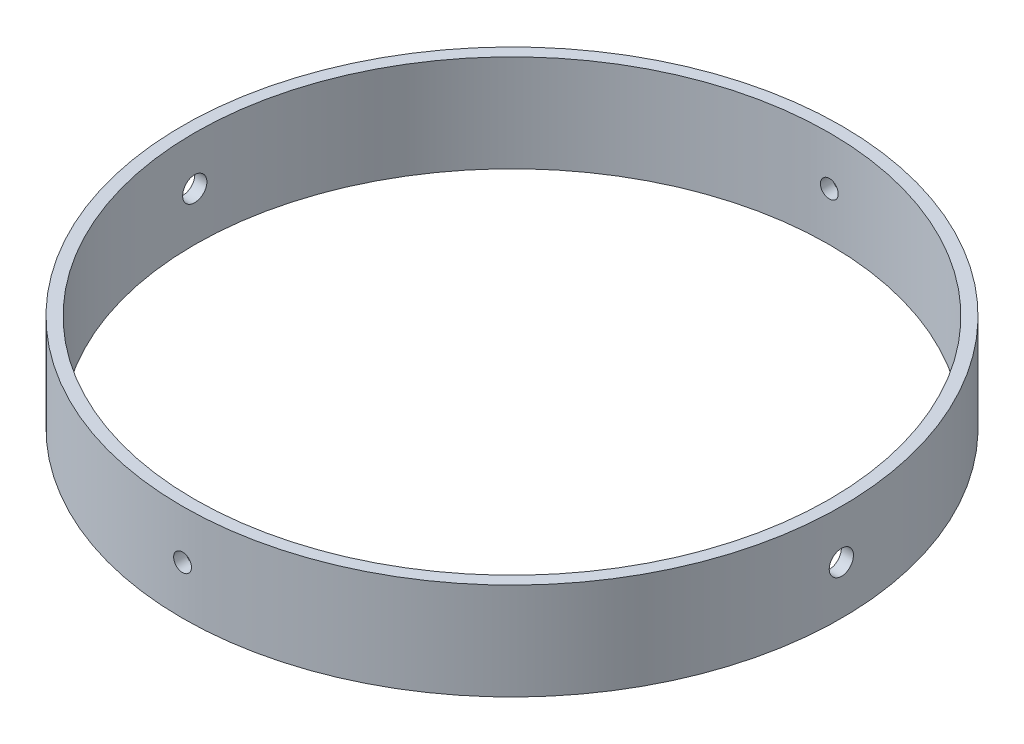
SolidWorks part; units mm, degrees
ref_plane "Front Plane" through (0, 0, 0) normal (0, 0, 1) x (1, 0, 0)
ref_plane "Top Plane" through (0, 0, 0) normal (0, 1, 0) x (1, 0, 0)
ref_plane "Right Plane" through (0, 0, 0) normal (1, 0, 0) x (0, 0, -1)
sketch "Sketch1" plane through (0, 0, 0) normal (0, 1, 0) x (1, 0, 0)
  circle A0 centre (0, 0) radius 86.36
  circle A1 centre (0, 0) radius 83.185
  dimension "D1" = 172.72
  dimension "D2" = 166.37
extrude "Boss-Extrude1" add sketch "Sketch1" along normal blind 25.4
sketch "Sketch2" plane through (0, 0, 0) normal (1, 0, 0) x (0, 0, -1)
  circle A0 centre (0, 12.7) radius 3.175
  dimension "D1" = 6.35
extrude "Cut-Extrude1" cut sketch "Sketch2" against normal through all and the other way through all
sketch "Sketch3" plane through (0, 0, 0) normal (0, 0, 1) x (1, 0, 0)
  circle A0 centre (0, 12.7) radius 2.3368
  dimension "D1" = 4.6736
extrude "Cut-Extrude2" cut sketch "Sketch3" against normal through all and the other way through all
